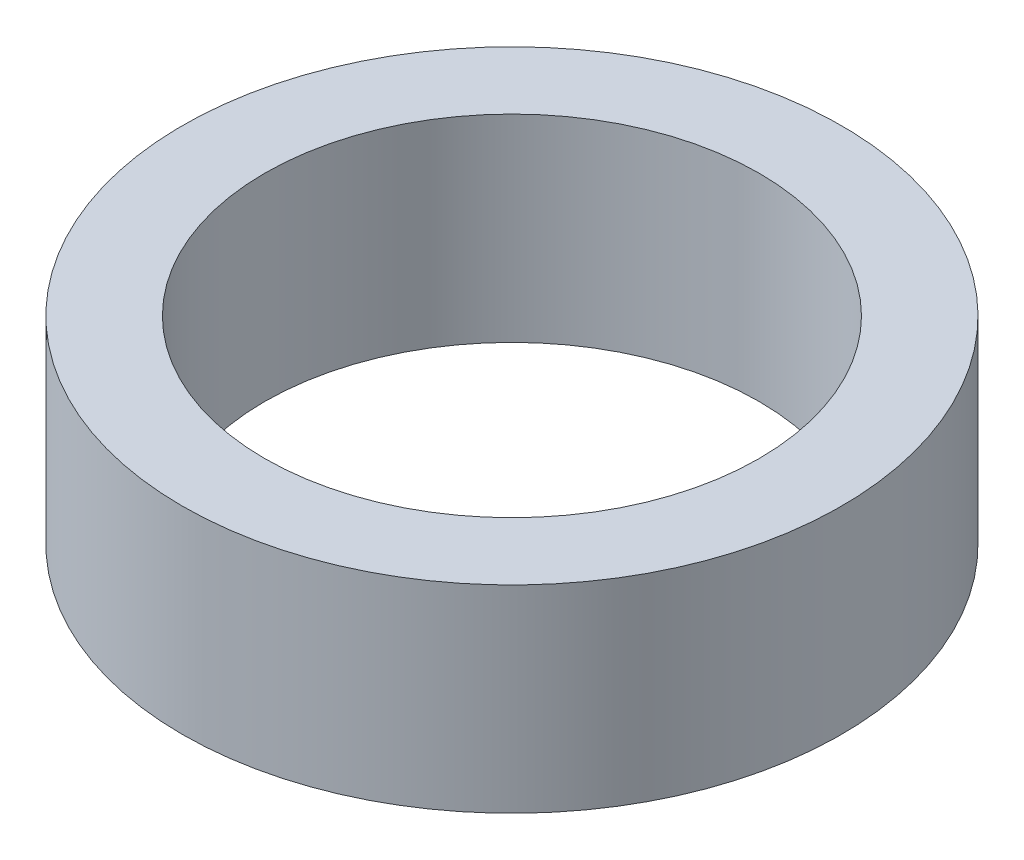
SolidWorks part; units mm, degrees
ref_plane "Front Plane" through (0, 0, 0) normal (0, 0, 1) x (1, 0, 0)
ref_plane "Top Plane" through (0, 0, 0) normal (0, 1, 0) x (1, 0, 0)
ref_plane "Right Plane" through (0, 0, 0) normal (1, 0, 0) x (0, 0, -1)
sketch "Sketch1" plane through (0, 0, 0) normal (0, 1, 0) x (1, 0, 0)
  circle A0 centre (0, 0) radius 15
  circle A1 centre (0, 0) radius 20
extrude "Boss-Extrude1" add sketch "Sketch1" along normal blind 12
